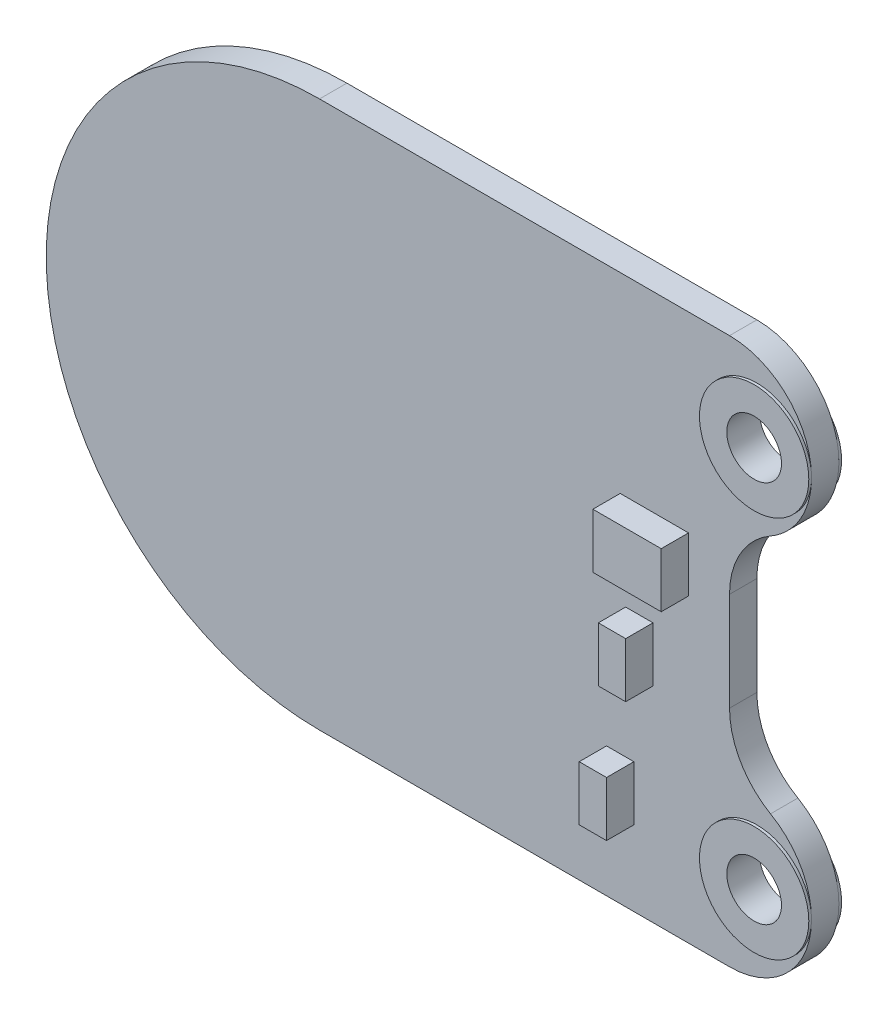
SolidWorks part; units mm, degrees
ref_plane "Front Plane" through (0, 0, 0) normal (0, 0, 1) x (1, 0, 0)
ref_plane "Top Plane" through (0, 0, 0) normal (0, 1, 0) x (1, 0, 0)
ref_plane "Right Plane" through (0, 0, 0) normal (1, 0, 0) x (0, 0, -1)
sketch "Sketch1" plane through (0, 0, 0) normal (0, 0, 1) x (1, 0, 0)
  line L0 (11, 4) -> (11, -4)
  line L1 (-4, 10) -> (11, 10)
  line L3 (-4, -10) -> (11, -10)
  line L5 (-10.563, 7.545) -> (12.9689, -9.2635) construction
  line L6 (-10.563, -7.545) -> (12.9689, 9.2635) construction
  arc A0 (-4, 10) -> (-4, -10) centre (-4, 0) ccw
  arc A1 (11, 4) -> (11, 10) centre (11, 7) ccw
  arc A2 (11, -10) -> (11, -4) centre (11, -7) ccw
  circle A5 centre (12, 7) radius 1
  circle A6 centre (12, -7) radius 1
  point P0 (0, 0)
  dimension "D3" = 20
  dimension "D4" = 2
  dimension "D1" = 6
  dimension "D2" = 6
  dimension "D5" = 2
  dimension "D6" = 1
  dimension "D7" = 1
extrude "Boss-Extrude1" add sketch "Sketch1" along normal blind 1
fillet "Fillet1" radius 3 2 edges at (11, -4, 0.5) (11, 4, 0.5)
sketch "Sketch2" plane through (0, 0, 1) normal (0, 0, 1) x (1, 0, 0)
  circle A0 centre (12, 7) radius 2
  circle A1 centre (12, -7) radius 2
  circle A2 centre (12, 7) radius 1
  circle A3 centre (12, -7) radius 1
  dimension "D1" = 4
  dimension "D2" = 4
extrude "Boss-Extrude2" add sketch "Sketch2" along normal blind 0.1 and the other way blind 1.1 contours A0 | A1
sketch "Sketch3" plane through (0, 0, 1.1) normal (0, 0, 1) x (1, 0, 0)
  circle A0 centre (12, 7) radius 1
  circle A1 centre (12, -7) radius 1
  dimension "D1" = 2
  dimension "D2" = 2
extrude "Cut-Extrude1" cut sketch "Sketch3" against normal blind 2
sketch "Sketch4" plane through (0, 0, 1) normal (0, 0, 1) x (1, 0, 0)
  line L0 (11, 10) -> (-4, 10) construction
  line L1 (7, 3) -> (9.5, 3)
  line L2 (7, 3) -> (7, 1)
  line L3 (7, 1) -> (9.5, 1)
  line L4 (9.5, 3) -> (9.5, 1)
  line L5 (7, 3) -> (9.5, 1) construction
  line L6 (7, 1) -> (9.5, 3) construction
  line L7 (7.2, -0.5) -> (8.2, -0.5)
  line L8 (7.2, -0.5) -> (7.2, -2.5)
  line L9 (7.2, -2.5) -> (8.2, -2.5)
  line L10 (8.2, -0.5) -> (8.2, -2.5)
  line L11 (7.2, -0.5) -> (8.2, -2.5) construction
  line L12 (7.2, -2.5) -> (8.2, -0.5) construction
  line L13 (6.5, -5.25) -> (7.5, -5.25)
  line L14 (6.5, -5.25) -> (6.5, -7.25)
  line L15 (6.5, -7.25) -> (7.5, -7.25)
  line L16 (7.5, -5.25) -> (7.5, -7.25)
  line L17 (6.5, -5.25) -> (7.5, -7.25) construction
  line L18 (6.5, -7.25) -> (7.5, -5.25) construction
  line L19 (-4, -10) -> (11, -10) construction
  line L20 (11, -1.8038) -> (11, 1.8038) construction
  point P0 (8.25, 2)
  point P5 (7.7, -1.5)
  point P10 (7, -6.25)
  dimension "D1" = 2.5
  dimension "D2" = 2
  dimension "D3" = 2
  dimension "D4" = 1
  dimension "D5" = 1
  dimension "D6" = 2
  dimension "D7" = 7
  dimension "D8" = 7.5
  dimension "D9" = 2.75
  dimension "D10" = 3.5
  dimension "D11" = 2.8
  dimension "D12" = 1.5
extrude "Boss-Extrude3" add sketch "Sketch4" along normal blind 1
